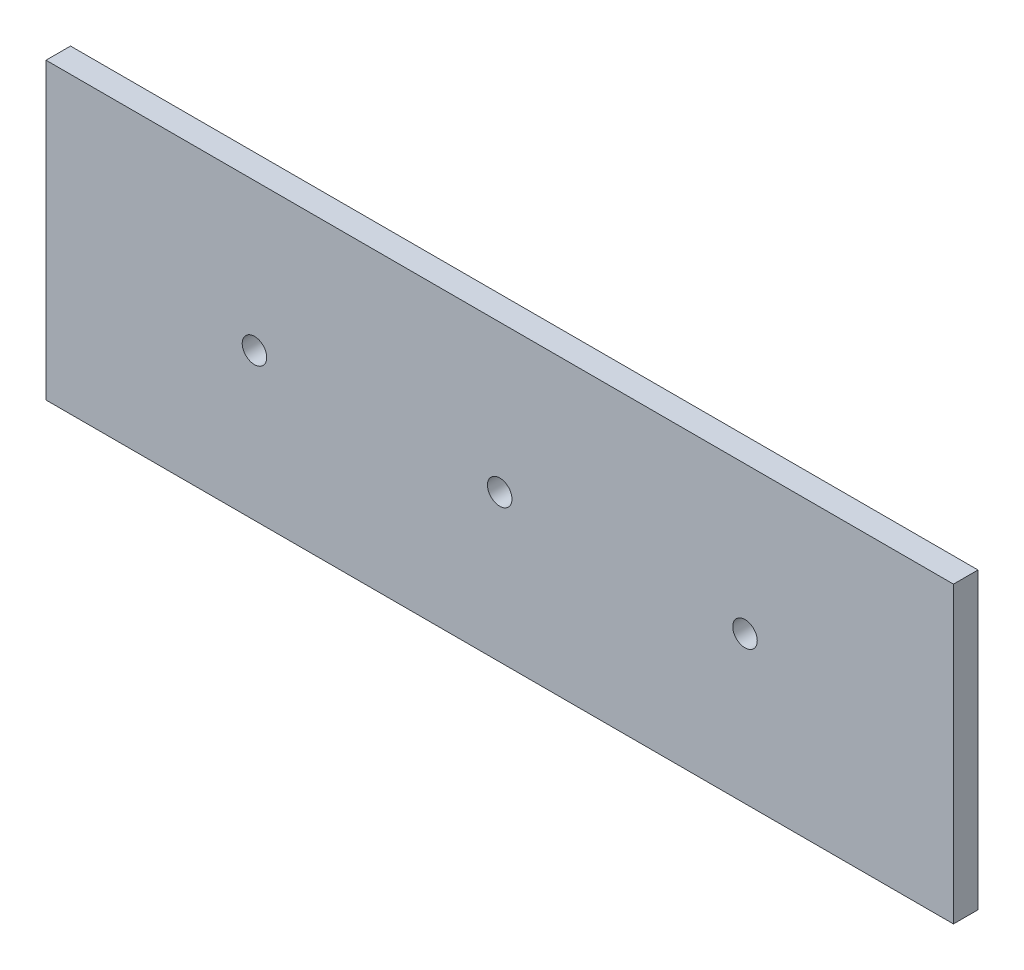
SolidWorks part; units mm, degrees
ref_plane "Alzado" through (0, 0, 0) normal (0, 0, 1) x (1, 0, 0)
ref_plane "Planta" through (0, 0, 0) normal (0, 1, 0) x (1, 0, 0)
ref_plane "Vista lateral" through (0, 0, 0) normal (1, 0, 0) x (0, 0, -1)
sketch "Croquis1" plane through (0, 0, 0) normal (0, 0, 1) x (1, 0, 0)
  line L1 (-117.475, 38.1) -> (117.475, 38.1)
  line L2 (-117.475, 38.1) -> (-117.475, -38.1)
  line L3 (-117.475, -38.1) -> (117.475, -38.1)
  line L4 (117.475, 38.1) -> (117.475, -38.1)
  line L5 (-117.475, 38.1) -> (117.475, -38.1) construction
  line L6 (-117.475, -38.1) -> (117.475, 38.1) construction
  point P0 (0, 0)
  dimension "D1" = 234.95
  dimension "D2" = 76.2
extrude "Saliente-Extruir1" add sketch "Croquis1" along normal blind 6.35
sketch "Croquis2" plane through (0, 0, 6.35) normal (0, 0, 1) x (1, 0, 0)
  line L0 (0, 38.1) -> (0, -38.1)
  line L1 (117.475, 38.1) -> (-117.475, 38.1) construction
  line L2 (-117.475, -38.1) -> (117.475, -38.1) construction
  line L3 (0, 0) -> (-63.5, 0) construction
  line L4 (0, 0) -> (63.5, 0) construction
  circle A0 centre (0, 0) radius 3.175
  circle A1 centre (-63.5, 0) radius 3.175
  circle A2 centre (63.5, 0) radius 3.175
  dimension "D1" = 6.35
  dimension "D3" = 6.35
  dimension "D5" = 6.35
  dimension "D2" = 63.5
  dimension "D4" = 63.5
extrude "Cortar-Extruir1" cut sketch "Croquis2" against normal through all contours L0 A0 | L0 A0 | A1 | A2
